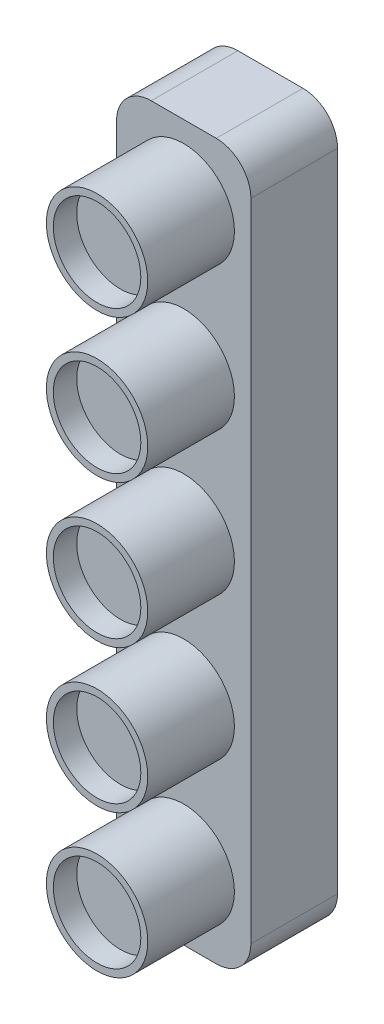
SolidWorks part; units mm, degrees
ref_plane "Ebene vorne" through (0, 0, 0) normal (0, 0, 1) x (1, 0, 0)
ref_plane "Ebene oben" through (0, 0, 0) normal (0, 1, 0) x (1, 0, 0)
ref_plane "Ebene rechts" through (0, 0, 0) normal (1, 0, 0) x (0, 0, -1)
sketch "Sketch1" plane through (0, 0, 0) normal (0, 0, 1) x (1, 0, 0)
  line L1 (0, 0) -> (-165, 0) construction
  line L2 (0, 0) -> (0, 165) construction
  line L3 (0, 165) -> (-165, 165) construction
  line L4 (-165, 0) -> (-165, 165) construction
  line L5 (-165, 165) -> (-149.5, 165)
  line L6 (-165, 165) -> (-165, 82.5)
  line L7 (-165, 82.5) -> (-149.5, 82.5)
  line L8 (-149.5, 165) -> (-149.5, 82.5)
  dimension "D1" = 165
  dimension "D2" = 165
  dimension "D3" = 82.5
  dimension "D4" = 15.5
extrude "Boss-Extrude1" add sketch "Sketch1" along normal blind 20
sketch "Sketch2" plane through (0, 0, 20) normal (0, 0, 1) x (1, 0, 0)
  line L0 (-165, 123.75) -> (-149.5, 123.75) construction
  line L1 (-165, 165) -> (-149.5, 165)
  line L2 (-165, 165) -> (-165, 82.5)
  line L3 (-165, 82.5) -> (-149.5, 82.5)
  line L4 (-149.5, 165) -> (-149.5, 82.5)
  circle A0 centre (-157.25, 156.75) radius 5.85
  circle A1 centre (-157.25, 140.25) radius 5.85
  circle A2 centre (-157.25, 156.75) radius 5.05
  circle A3 centre (-157.25, 140.25) radius 5.05
  circle A4 centre (-157.25, 107.25) radius 5.85
  circle A5 centre (-157.25, 107.25) radius 5.05
  circle A6 centre (-157.25, 90.75) radius 5.85
  circle A7 centre (-157.25, 90.75) radius 5.05
  circle A8 centre (-157.25, 123.75) radius 5.85
  circle A9 centre (-157.25, 123.75) radius 5.05
  point P13 (-157.25, 123.75)
  line M10 (-165, 165) -> (-165, 82.5)
  line M11 (-165, 82.5) -> (-149.5, 82.5)
  line M12 (-149.5, 82.5) -> (-149.5, 165)
  line M13 (-149.5, 165) -> (-165, 165)
  dimension "D1" = 16.5
  dimension "D3" = 11.7
  dimension "D4" = 11.7
  dimension "D5" = 10.1
  dimension "D7" = 11.7
  dimension "D2" = 16.5
extrude "Cut-Extrude1" cut sketch "Sketch2" against normal blind 10 contours L0 A8 L4 A0 A1 M10 M13 | L0 L2 A8 A4 A6 M11 M12 | A7 | A5 | L0 A9 | A9 L0 | A3 | A2
sketch "Sketch3" plane through (0, 0, 0) normal (0, 0, -1) x (-1, 0, 0)
  line L0 (149.5, 123.75) -> (165, 123.75) construction
  line L1 (149.5, 82.5) -> (149.5, 165) construction
  line L2 (165, 165) -> (165, 82.5) construction
  circle A0 centre (157.25, 156.75) radius 2.5
  circle A1 centre (157.25, 140.25) radius 2.5
  circle A2 centre (157.25, 123.75) radius 2.5
  circle A3 centre (157.25, 107.25) radius 2.5
  circle A4 centre (157.25, 90.75) radius 2.5
  dimension "D1" = 5
  dimension "D2" = 5
  dimension "D3" = 5
  dimension "D4" = 16.5
  dimension "D5" = 16.5
extrude "Cut-Extrude2" [suppressed] cut sketch "Sketch3" against normal blind 5
fillet "Fillet1" radius 4 4 edges at (-149.5, 165, 5) (-165, 165, 5) (-165, 82.5, 5) (-149.5, 82.5, 5)
ref_plane "Ebene1" through (0, 0, -2.5) normal (0, 0, -1) x (-1, 0, 0)
sketch "Skizze1" plane through (0, 0, -2.5) normal (0, 0, -1) x (-1, 0, 0)
  line L0 (149.5, 138.75) -> (149.5, 128.75)
  line L1 (149.5, 165) -> (165, 165)
  line L2 (149.5, 165) -> (149.5, 148.75)
  line L3 (149.5, 82.5) -> (165, 82.5)
  line L4 (165, 165) -> (165, 138.75)
  line L5 (165, 128.75) -> (165, 118.75)
  line L6 (149.5, 118.75) -> (149.5, 108.75)
  line L7 (153.5, 165) -> (161, 165) construction
  line L8 (161, 82.5) -> (153.5, 82.5) construction
  line L9 (149.5, 86.5) -> (149.5, 161) construction
  line L10 (165, 161) -> (165, 86.5) construction
  line L11 (165, 108.75) -> (165, 82.5)
  line L12 (149.5, 148.75) -> (149, 148.75)
  line L14 (149.5, 138.75) -> (149, 138.75)
  line L15 (149, 148.75) -> (149, 138.75)
  line L16 (149.5, 128.75) -> (149, 128.75)
  line L18 (149.5, 118.75) -> (149, 118.75)
  line L19 (149, 128.75) -> (149, 118.75)
  line L20 (149.5, 108.75) -> (149, 108.75)
  line L22 (149.5, 98.75) -> (149, 98.75)
  line L23 (149, 108.75) -> (149, 98.75)
  line L24 (165, 118.75) -> (165.5, 118.75)
  line L26 (165, 108.75) -> (165.5, 108.75)
  line L27 (165.5, 118.75) -> (165.5, 108.75)
  line L28 (165, 138.75) -> (165.5, 138.75)
  line L30 (165, 128.75) -> (165.5, 128.75)
  line L31 (165.5, 138.75) -> (165.5, 128.75)
  line L32 (149.5, 98.75) -> (149.5, 82.5)
  dimension "D1" = 0.5
  dimension "D2" = 10
  dimension "D3" = 10
  dimension "D4" = 10
  dimension "D5" = 10
  dimension "D6" = 10
  dimension "D7" = 0.5
  dimension "D8" = 16.25
sketch "Skizze2" plane through (0, 0, 0) normal (0, 0, -1) x (-1, 0, 0)
  line L0 (153.5, 165) -> (161, 165) construction
  line L1 (153.5, 165) -> (161, 165)
  line L2 (149.5, 161) -> (149.5, 86.5)
  line L3 (153.5, 82.5) -> (161, 82.5)
  line L4 (165, 161) -> (165, 86.5)
  line L5 (149.5, 86.5) -> (149.5, 161) construction
  line L6 (165, 161) -> (165, 86.5) construction
  line L7 (161, 82.5) -> (153.5, 82.5) construction
  arc A0 (149.5, 86.5) -> (153.5, 82.5) centre (153.5, 86.5) ccw
  arc A1 (153.5, 165) -> (149.5, 161) centre (153.5, 161) ccw
  arc A2 (161, 165) -> (165, 161) centre (161, 161) cw
  arc A3 (161, 82.5) -> (165, 86.5) centre (161, 86.5) ccw
  dimension "D1" = 4
  dimension "D2" = 4
sketch "Skizze3" plane through (0, 0, 10) normal (0, 0, 1) x (1, 0, 0)
  circle A0 centre (-157.25, 156.75) radius 5.1
  circle A1 centre (-157.25, 140.25) radius 5.1
  circle A2 centre (-157.25, 123.75) radius 5.05
  circle A3 centre (-157.25, 107.25) radius 5.05
  circle A4 centre (-157.25, 90.75) radius 5.1
  circle A5 centre (-157.25, 107.25) radius 5.05 construction
  circle A6 centre (-157.25, 123.75) radius 5.05 construction
  dimension "D1" = 10.2
  dimension "D2" = 10.2
  dimension "D3" = 10.2
extrude "Aufsatz-Linear austragen1" add sketch "Skizze3" along normal blind 7.3
sketch "Skizze4" plane through (0, 0, 0) normal (0, 0, -1) x (-1, 0, 0)
  line L8 (161, 163) -> (153.5, 163)
  line L9 (151.5, 161) -> (151.5, 86.5)
  line L10 (153.5, 84.5) -> (161, 84.5)
  line L11 (163, 86.5) -> (163, 161)
  line L12 (161, 163) -> (153.5, 163)
  line L13 (151.5, 161) -> (151.5, 86.5)
  line L14 (153.5, 84.5) -> (161, 84.5)
  line L15 (163, 86.5) -> (163, 161)
  arc A8 (153.5, 163) -> (151.5, 161) centre (153.5, 161) ccw
  arc A9 (151.5, 86.5) -> (153.5, 84.5) centre (153.5, 86.5) ccw
  arc A10 (161, 84.5) -> (163, 86.5) centre (161, 86.5) ccw
  arc A11 (163, 161) -> (161, 163) centre (161, 161) ccw
  arc A12 (153.5, 163) -> (151.5, 161) centre (153.5, 161) ccw
  arc A13 (151.5, 86.5) -> (153.5, 84.5) centre (153.5, 86.5) ccw
  arc A14 (161, 84.5) -> (163, 86.5) centre (161, 86.5) ccw
  arc A15 (163, 161) -> (161, 163) centre (161, 161) ccw
  dimension "D1" = 2
extrude "Schnitt-Linear austragen1" cut sketch "Skizze4" against normal blind 9
